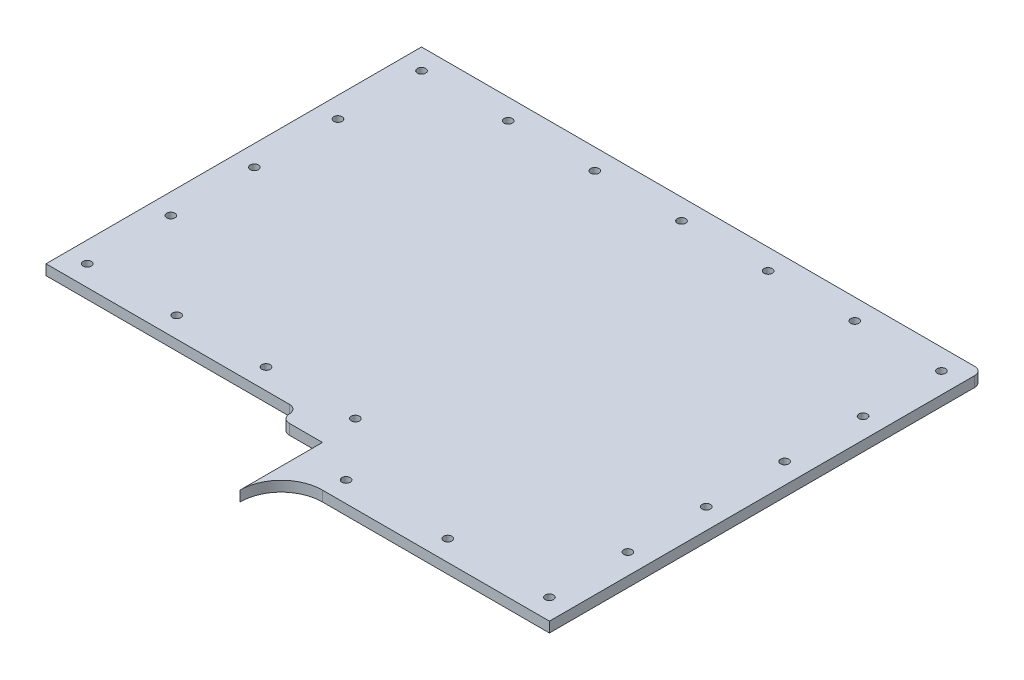
SolidWorks part; units mm, degrees
ref_plane "Front Plane" through (0, 0, 0) normal (0, 0, 1) x (1, 0, 0)
ref_plane "Top Plane" through (0, 0, 0) normal (0, 1, 0) x (1, 0, 0)
ref_plane "Right Plane" through (0, 0, 0) normal (1, 0, 0) x (0, 0, -1)
other "Bounding Box"
ref_plane "Default Plane" through (-8.9266, -12.7485, 0) normal (-0.1736, 0.9848, 0) x (0.9848, 0.1736, 0)
sketch "Sketch1" plane through (0, 0, 0) normal (0, 1, 0) x (1, 0, 0)
  line B0 (8.89, -66.675) -> (43.815, -66.675)
  line B1 (43.815, -66.675) -> (43.815, -1.27)
  line B2 (42.545, 0) -> (-42.545, 0)
  line B3 (-42.545, 0) -> (-42.545, -57.785)
  line B4 (-42.545, -57.785) -> (-5.08, -57.785)
  line B5 (-2.54, -60.325) -> (2.54, -60.325)
  line B6 (2.54, -60.325) -> (2.54, -73.025)
  arc B7 (8.89, -66.675) -> (2.54, -73.025) centre (8.89, -73.025) ccw
  arc B8 (43.815, -1.27) -> (42.545, 0) centre (42.5797, -1.2353) ccw
  arc B9 (-5.08, -57.785) -> (-3.81, -59.055) centre (-5.08, -59.055) cw
  arc B10 (-3.81, -59.055) -> (-2.54, -60.325) centre (-2.54, -59.055) ccw
sketch_block_instance "Left side Top plate-1"
sketch_block "Left side Top plate"
extrude "Boss-Extrude1" add sketch "Sketch1" along normal blind 1.5875
sketch "Sketch2" plane through (0, 1.5875, 0) normal (0, 1, 0) x (-1, 0, 0)
  line L0 (-9.3488, 63.5) -> (-40.64, 63.5) construction
  line L1 (-40.64, 63.5) -> (-40.64, 3.175) construction
  line L2 (-40.64, 3.175) -> (39.37, 3.175) construction
  line L3 (39.37, 3.175) -> (39.37, 54.61) construction
  line L4 (39.37, 54.61) -> (-1.8892, 54.61) construction
  line L5 (-1.8892, 54.61) -> (-9.3488, 63.5) construction
  line L6 (-42.545, 0) -> (42.545, 0) construction
  line L7 (42.545, 0) -> (42.545, 57.785) construction
  line L8 (42.545, 57.785) -> (5.08, 57.785) construction
  line L9 (-8.89, 66.675) -> (-43.815, 66.675) construction
  line L10 (-43.815, 66.675) -> (-43.815, 1.27) construction
  circle A0 centre (39.37, 3.175) radius 0.635
  circle A1 centre (26.035, 3.175) radius 0.635
  circle A2 centre (12.7, 3.175) radius 0.635
  circle A3 centre (-0.635, 3.175) radius 0.635
  circle A4 centre (-13.97, 3.175) radius 0.635
  circle A5 centre (-27.305, 3.175) radius 0.635
  circle A6 centre (-40.64, 3.175) radius 0.635
  circle A7 centre (39.37, 16.0338) radius 0.635
  circle A8 centre (39.37, 28.8925) radius 0.635
  circle A9 centre (39.37, 41.7513) radius 0.635
  circle A11 centre (-40.64, 15.24) radius 0.635
  circle A12 centre (-40.64, 27.305) radius 0.635
  circle A13 centre (-40.64, 39.37) radius 0.635
  circle A14 centre (-40.64, 51.435) radius 0.635
  circle A15 centre (-40.64, 63.5) radius 0.635
  circle A16 centre (-24.9944, 63.5) radius 0.635
  circle A17 centre (-9.3488, 63.5) radius 0.635
  circle A18 centre (-1.8892, 54.61) radius 0.635
  circle A19 centre (11.8639, 54.61) radius 0.635
  circle A20 centre (25.6169, 54.61) radius 0.635
  circle A21 centre (39.37, 54.61) radius 0.635
  circle A22 centre (39.37, 54.61) radius 0.635 [skipped]
  dimension "D8" = 1.27
  dimension "D14" = 12.8588
  dimension "D1" = 3.175
  dimension "D2" = 3.175
  dimension "D3" = 3.175
  dimension "D4" = 3.175
  dimension "D5" = 3.175
  dimension "D6" = 3.175
  dimension "D7" = 130
  dimension "D9" = 7
  dimension "D10" = 5
  dimension "D11" = 6
  dimension "D12" = 3
  dimension "D13" = 4
extrude "Cut-Extrude1" cut sketch "Sketch2" against normal through all both and the other way through all
